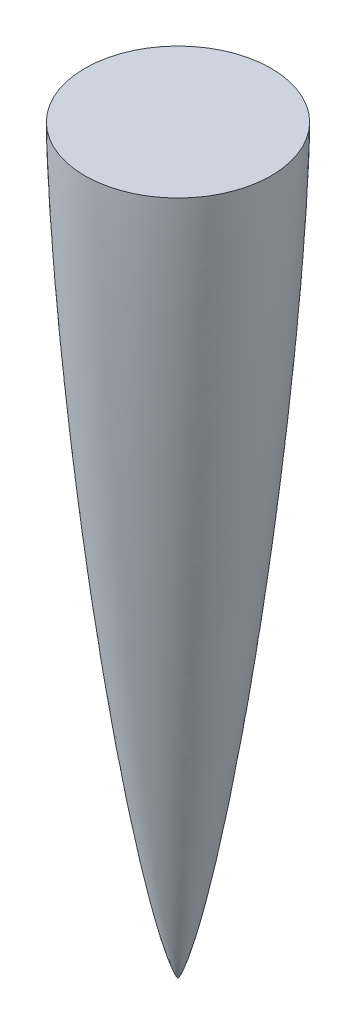
SolidWorks part; units mm, degrees
ref_plane "Front Plane" through (0, 0, 0) normal (1, 0, 0) x (0, 1, 0)
ref_plane "Top Plane" through (0, 0, 0) normal (0, 0, 1) x (0, 1, 0)
ref_plane "Right Plane" through (0, 0, 0) normal (0, 1, 0) x (-1, 0, 0)
sketch "Sketch4" plane through (0, 0, 0) normal (1, 0, 0) x (0, 1, 0)
  line L0 (-54.2913, 0) -> (459.9865, 0) construction
  line L1 (406.4, 51.054) -> (406.4, 0)
  line L4 (0, 0) -> (406.4, 0)
  spline S0 degree 4 poles (0, 0) (0.0034, 0.0106) (0.0126, 0.0306) (0.0392, 0.0664) (0.0816, 0.114) (0.1343, 0.1641) (0.2107, 0.2299) (0.3232, 0.3172) (0.494, 0.4361) (0.7618, 0.6034) (1.193, 0.8449) (1.9162, 1.2068) (3.1954, 1.7726) (5.5461, 2.6826) (9.8579, 4.1259) (17.1311, 6.222) (29.9883, 9.4281) (47.9423, 13.2637) (70.0263, 17.4144) (95.1028, 21.6221) (120.2374, 25.4635) (145.4165, 29.0011) (170.631, 32.2756) (195.8755, 35.3102) (221.1459, 38.1198) (246.4396, 40.7111) (268.5903, 42.7883) (287.5891, 44.429) (303.4295, 45.6989) (316.1065, 46.6539) (328.7882, 47.5449) (341.4746, 48.3675) (352.5791, 49.0223) (362.1002, 49.5318) (370.0364, 49.9182) (376.3865, 50.2023) (382.4297, 50.4464) (388.1659, 50.6517) (392.9546, 50.7994) (396.7956, 50.9004) (399.9968, 50.9708) (402.2377, 51.011) (404.1587, 51.0382) (405.4394, 51.0494) (406.0798, 51.054) (406.4, 51.054) knots 0 0 0 0 0 0.000108 0.000215 0.00043 0.000622 0.000814 0.001197 0.001817 0.002648 0.003888 0.006009 0.00969 0.016266 0.02843 0.05028 0.083391 0.145299 0.207207 0.269115 0.331023 0.392931 0.454839 0.516748 0.578656 0.640564 0.702472 0.733426 0.76438 0.795334 0.826288 0.857242 0.888196 0.903673 0.91915 0.934627 0.950104 0.962578 0.975052 0.981289 0.987526 0.993763 0.996882 1 1 1 1 1 construction
  spline S1 degree 4 poles (0, 0) (0.0034, 0.0106) (0.0126, 0.0306) (0.0392, 0.0664) (0.0816, 0.114) (0.1343, 0.1641) (0.2107, 0.2299) (0.3232, 0.3172) (0.494, 0.4361) (0.7618, 0.6034) (1.193, 0.8449) (1.9162, 1.2068) (3.1954, 1.7726) (5.5461, 2.6826) (9.8579, 4.1259) (17.1311, 6.222) (29.9883, 9.4281) (47.9423, 13.2637) (70.0263, 17.4144) (95.1028, 21.6221) (120.2374, 25.4635) (145.4165, 29.0011) (170.631, 32.2756) (195.8755, 35.3102) (221.1459, 38.1198) (246.4396, 40.7111) (268.5903, 42.7883) (287.5891, 44.429) (303.4295, 45.6989) (316.1065, 46.6539) (328.7882, 47.5449) (341.4746, 48.3675) (352.5791, 49.0223) (362.1002, 49.5318) (370.0364, 49.9182) (376.3865, 50.2023) (382.4297, 50.4464) (388.1659, 50.6517) (392.9546, 50.7994) (396.7956, 50.9004) (399.9968, 50.9708) (402.2377, 51.011) (404.1587, 51.0382) (405.4394, 51.0494) (406.0798, 51.054) (406.4, 51.054) knots 0 0 0 0 0 0.000108 0.000215 0.00043 0.000622 0.000814 0.001197 0.001817 0.002648 0.003888 0.006009 0.00969 0.016266 0.02843 0.05028 0.083391 0.145299 0.207207 0.269115 0.331023 0.392931 0.454839 0.516748 0.578656 0.640564 0.702472 0.733426 0.76438 0.795334 0.826288 0.857242 0.888196 0.903673 0.91915 0.934627 0.950104 0.962578 0.975052 0.981289 0.987526 0.993763 0.996882 1 1 1 1 1
  dimension "D1" = 406.4
  dimension "D2" = 51.054
revolve "Revolve2" add sketch "Sketch4" angle 360 about L0
equation "\"D\"= 4.02in"
equation "\"L\"= 16in"
equation "\"R\"= 2.01in"
